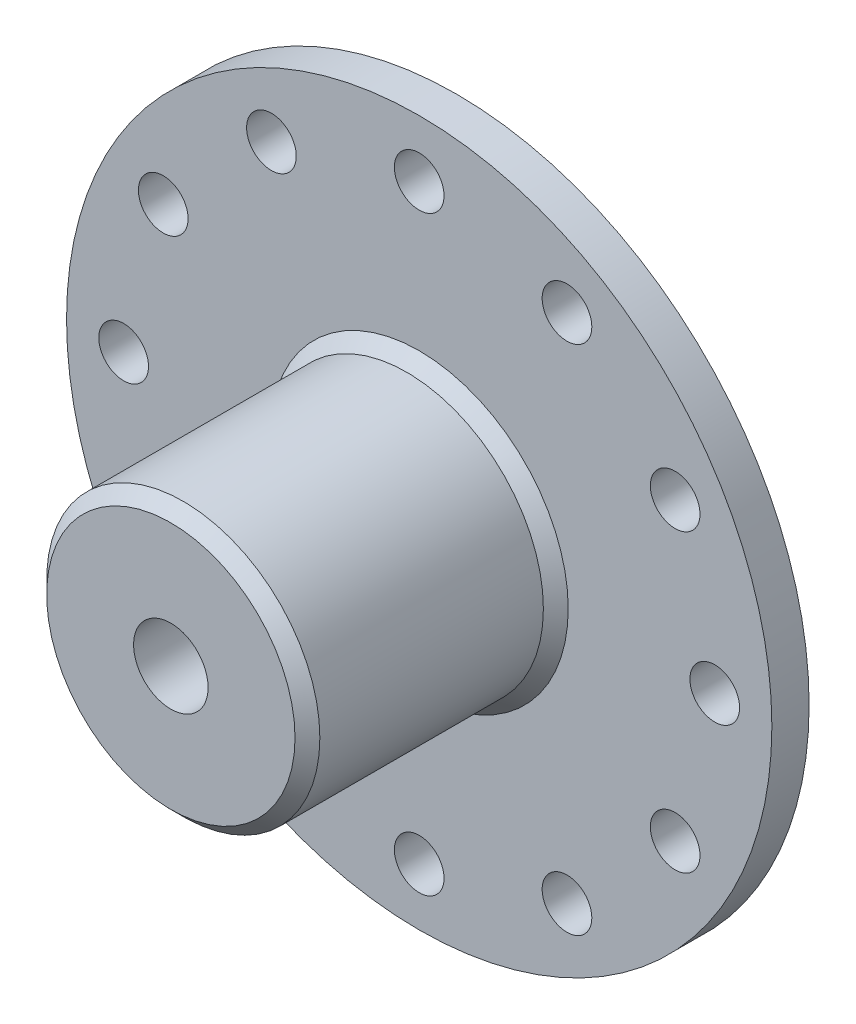
SolidWorks part; units mm, degrees
ref_plane "Front Plane" through (0, 0, 0) normal (0, 0, 1) x (1, 0, 0)
ref_plane "Top Plane" through (0, 0, 0) normal (0, 1, 0) x (1, 0, 0)
ref_plane "Right Plane" through (0, 0, 0) normal (1, 0, 0) x (0, 0, -1)
sketch "Sketch1" plane through (0, 0, 0) normal (0, 0, 1) x (1, 0, 0)
  circle A0 centre (0, 0) radius 28.4
  circle A1 centre (0, 0) radius 28.4 construction
extrude "Boss-Extrude1" add sketch "Sketch1" along normal blind 3
sketch "Sketch2" plane through (0, 0, 3) normal (0, 0, 1) x (1, 0, 0)
  circle A0 centre (0, 0) radius 11
  dimension "D1" = 22
extrude "Boss-Extrude2" add sketch "Sketch2" along normal blind 20
sketch "Sketch3" plane through (0, 0, 23) normal (0, 0, 1) x (1, 0, 0)
  circle A0 centre (0, 0) radius 3
  dimension "D1" = 6
extrude "Cut-Extrude1" cut sketch "Sketch3" against normal through all
sketch "Sketch4" plane through (0, 0, 0) normal (0, 1, 0) x (1, 0, 0)
  circle A0 centre (0, -15) radius 2
  dimension "D1" = 4
  dimension "D2" = 15
extrude "Cut-Extrude2" cut sketch "Sketch4" against normal blind 15
chamfer "Chamfer1" distance 1 angle 45 2 edges at (11, 0, 3) (11, 0, 23)
sketch "Sketch5" plane through (0, 0, 3) normal (0, 0, 1) x (1, 0, 0)
  circle A0 centre (11.9, 20.6114) radius 2
  circle A1 centre (0, 0) radius 28.4
  circle A2 centre (0, 0) radius 28.4
  dimension "D2" = 4
  dimension "D1" = 0
extrude "Cut-Extrude5" cut sketch "Sketch5" against normal through all contours A0
pattern_circular "CirPattern2" count 12 over 360 about axis through (0, 0, 0) along (0, 0, 1) of "Cut-Extrude5"
